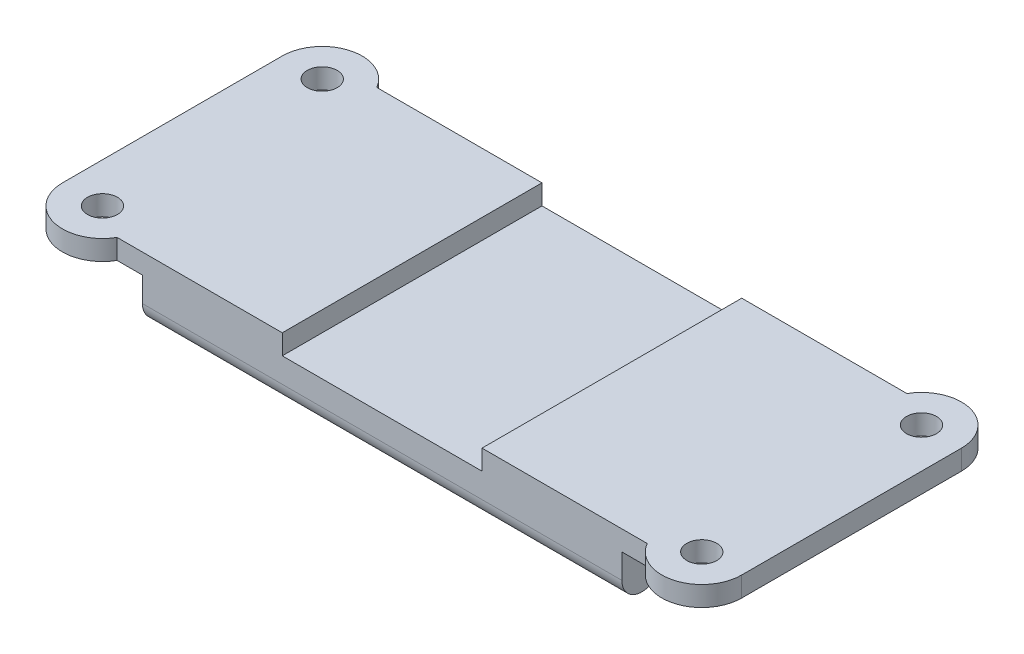
SolidWorks part; units mm, degrees
material "PEI"
ref_plane "Front Plane" through (0, 0, 0) normal (0, 0, 1) x (1, 0, 0)
ref_plane "Top Plane" through (0, 0, 0) normal (0, 1, 0) x (1, 0, 0)
ref_plane "Right Plane" through (0, 0, 0) normal (1, 0, 0) x (0, 0, -1)
sketch "Sketch1" plane through (0, 0, 0) normal (0, 1, 0) x (1, 0, 0)
  line L1 (24, -13) -> (-24, -13)
  line L2 (24, -13) -> (24, 13)
  line L3 (24, 13) -> (-24, 13)
  line L4 (-24, -13) -> (-24, 13)
  line L5 (24, -13) -> (-24, 13) construction
  line L6 (24, 13) -> (-24, -13) construction
  point P0 (0, 0)
  dimension "D1" = 26
  dimension "D2" = 48
extrude "Boss-Extrude1" add sketch "Sketch1" against normal blind 8
sketch "Sketch2" plane through (24, 0, 0) normal (1, 0, 0) x (0, 0, -1)
  line L0 (-13, -8) -> (-8, -5)
  line L1 (-8, -5) -> (8, -5)
  line L2 (0, -5) -> (0, -8)
  line L3 (13, -8) -> (8, -5)
  line L4 (13, 0) -> (-13, 0)
  line L5 (-13, 0) -> (-13, -8)
  line L6 (-13, -8) -> (13, -8)
  line L7 (13, -8) -> (13, 0)
  line L8 (13, 0) -> (-13, 0)
  line L9 (-13, 0) -> (-13, -8)
  line L10 (-13, -8) -> (13, -8)
  line L11 (13, -8) -> (13, 0)
  line M7 (-13, -8) -> (13, -8)
  dimension "D2" = 5
  dimension "D3" = 3
  dimension "D1" = 0
extrude "Cut-Extrude1" cut sketch "Sketch2" against normal through all and the other way through all contours L2 L1 L0 M7 | L3 L1 L2 M7
fillet "Fillet1" radius 2 4 edges at (0, -5, 8) (0, -5, -8) (0, -8, -13) (0, -8, 13)
sketch "Sketch3" plane through (0, 0, 13) normal (0, 0, 1) x (1, 0, 0)
  line L0 (-24, 0) -> (24, 0) construction
  line L1 (-10, 2) -> (10, 2)
  line L2 (-10, 2) -> (-10, -2)
  line L3 (-10, -2) -> (10, -2)
  line L4 (-24, 0) -> (-24, -4.4676)
  line L5 (-24, -4.4676) -> (24, -4.4676)
  line L6 (24, -4.4676) -> (24, 0)
  line L7 (24, 0) -> (-24, 0)
  line L8 (-24, 0) -> (-24, -4.4676)
  line L9 (-24, -4.4676) -> (24, -4.4676)
  line L10 (24, -4.4676) -> (24, 0)
  line L11 (24, 0) -> (-24, 0)
  line L12 (10, 2) -> (10, -2)
  line L13 (-10, 2) -> (10, -2) construction
  line L14 (-10, -2) -> (10, 2) construction
  line L15 (0, 0) -> (0, -4.4676)
  point P2 (0, 0)
  point P18 (0, 0)
  line M10 (24, 0) -> (-24, 0)
  dimension "D2" = 20
  dimension "D3" = 4
  dimension "D1" = 0
sketch "Sketch5" plane through (-24, 0, 0) normal (-1, 0, 0) x (0, 0, 1)
  line L1 (-13, 0) -> (13, 0)
  line L2 (-13, 0) -> (-13, -2)
  line L3 (-13, -2) -> (13, -2)
  line L4 (13, 0) -> (13, -2)
  line L6 (-13, 0) -> (-13, -4.4676)
  line L7 (-9.971, -6.1826) -> (-8.475, -5.285)
  line L8 (-7.446, -5) -> (7.446, -5)
  line L9 (8.475, -5.285) -> (9.971, -6.1826)
  line L10 (13, -4.4676) -> (13, 0)
  line L11 (13, 0) -> (-13, 0)
  line L12 (-13, 0) -> (-13, -4.4676)
  line L13 (-9.971, -6.1826) -> (-8.475, -5.285)
  line L14 (-7.446, -5) -> (7.446, -5)
  line L15 (8.475, -5.285) -> (9.971, -6.1826)
  line L16 (13, -4.4676) -> (13, 0)
  line L17 (13, 0) -> (-13, 0)
  arc A4 (-13, -4.4676) -> (-9.971, -6.1826) centre (-11, -4.4676) ccw
  arc A5 (-7.446, -5) -> (-8.475, -5.285) centre (-7.446, -7) ccw
  arc A6 (8.475, -5.285) -> (7.446, -5) centre (7.446, -7) ccw
  arc A7 (9.971, -6.1826) -> (13, -4.4676) centre (11, -4.4676) ccw
  arc A8 (-13, -4.4676) -> (-9.971, -6.1826) centre (-11, -4.4676) ccw
  arc A9 (-7.446, -5) -> (-8.475, -5.285) centre (-7.446, -7) ccw
  arc A10 (8.475, -5.285) -> (7.446, -5) centre (7.446, -7) ccw
  arc A11 (9.971, -6.1826) -> (13, -4.4676) centre (11, -4.4676) ccw
  line M13 (-13, 0) -> (-13, -4.4676)
  line M21 (13, -4.4676) -> (13, 0)
  line M22 (13, 0) -> (-13, 0)
  dimension "D2" = 2
  dimension "D1" = 0
extrude "Boss-Extrude2" add sketch "Sketch5" along normal blind 10 contours L3 M13 M21 M22
mirror "Mirror1" about plane through (0, 0, 0) normal (1, 0, 0) of "Boss-Extrude2"
sketch "Sketch6" plane through (0, 0, 0) normal (0, 1, 0) x (1, 0, 0)
  line L0 (0, 0) -> (-30, 0)
  line L1 (-30, 0) -> (-30, 11)
  line L2 (0, 0) -> (0, 13)
  line L4 (34, 13) -> (-34, 13)
  line L5 (-34, 13) -> (-34, -13)
  line L6 (-34, -13) -> (34, -13)
  line L7 (34, -13) -> (34, 13)
  line L8 (34, 13) -> (-34, 13)
  line L9 (-34, 13) -> (-34, -13)
  line L10 (-34, -13) -> (34, -13)
  line L11 (34, -13) -> (34, 13)
  circle A0 centre (-30, 11) radius 1.5
  circle A1 centre (-30, -11) radius 1.5
  circle A2 centre (30, -11) radius 1.5
  circle A3 centre (30, 11) radius 1.5
  dimension "D4" = 3
  dimension "D2" = 11
  dimension "D3" = 30
  dimension "D1" = 0
extrude "Cut-Extrude2" cut sketch "Sketch6" against normal blind 10
extrude "Cut-Extrude3" cut sketch "Sketch3" against normal through all contours L11 L15 L3 L12 | L15 L2 L3 M10
fillet "Fillet3" radius 2 4 edges at (34, -1, -13) (34, -1, 13) (-34, -1, -13) (-34, -1, 13)
sketch "Sketch7" plane through (0, 0, 0) normal (0, 1, 0) x (1, 0, 0)
  line L0 (0, -3.5572) -> (0, 3.5572) construction
  line L4 (-10, 13) -> (-32, 13)
  line L5 (-34, 11) -> (-34, -11)
  line L6 (-32, -13) -> (-10, -13)
  line L7 (-10, -13) -> (-10, 13)
  line L8 (-10, 13) -> (-32, 13)
  line L9 (-34, 11) -> (-34, -11)
  line L10 (-32, -13) -> (-10, -13)
  line L11 (-10, -13) -> (-10, 13)
  circle A0 centre (-30, 11) radius 4
  circle A1 centre (-30, -11) radius 4
  arc A2 (-32, 13) -> (-34, 11) centre (-32, 11) ccw
  arc A3 (-34, -11) -> (-32, -13) centre (-32, -11) ccw
  arc A4 (-32, 13) -> (-34, 11) centre (-32, 11) ccw
  arc A5 (-34, -11) -> (-32, -13) centre (-32, -11) ccw
  circle A6 centre (-30, 11) radius 1.5
  circle A7 centre (-30, -11) radius 1.5
  circle A8 centre (30, 11) radius 1.5
  circle A9 centre (30, 11) radius 4
  circle A10 centre (30, -11) radius 1.5
  circle A11 centre (30, -11) radius 4
  arc M8 (-32, 13) -> (-34, 11) centre (-32, 11) ccw
  arc M10 (-34, -11) -> (-32, -13) centre (-32, -11) ccw
  line M11 (-32, -13) -> (-10, -13)
  dimension "D2" = 8
  dimension "D3" = 8
  dimension "D4" = 3
  dimension "D5" = 3
  dimension "D1" = 0
extrude "Boss-Extrude3" add sketch "Sketch7" against normal blind 2 contours L8 A0 M8 | A1 M10 M11 | A9 A8 | A11 A10
